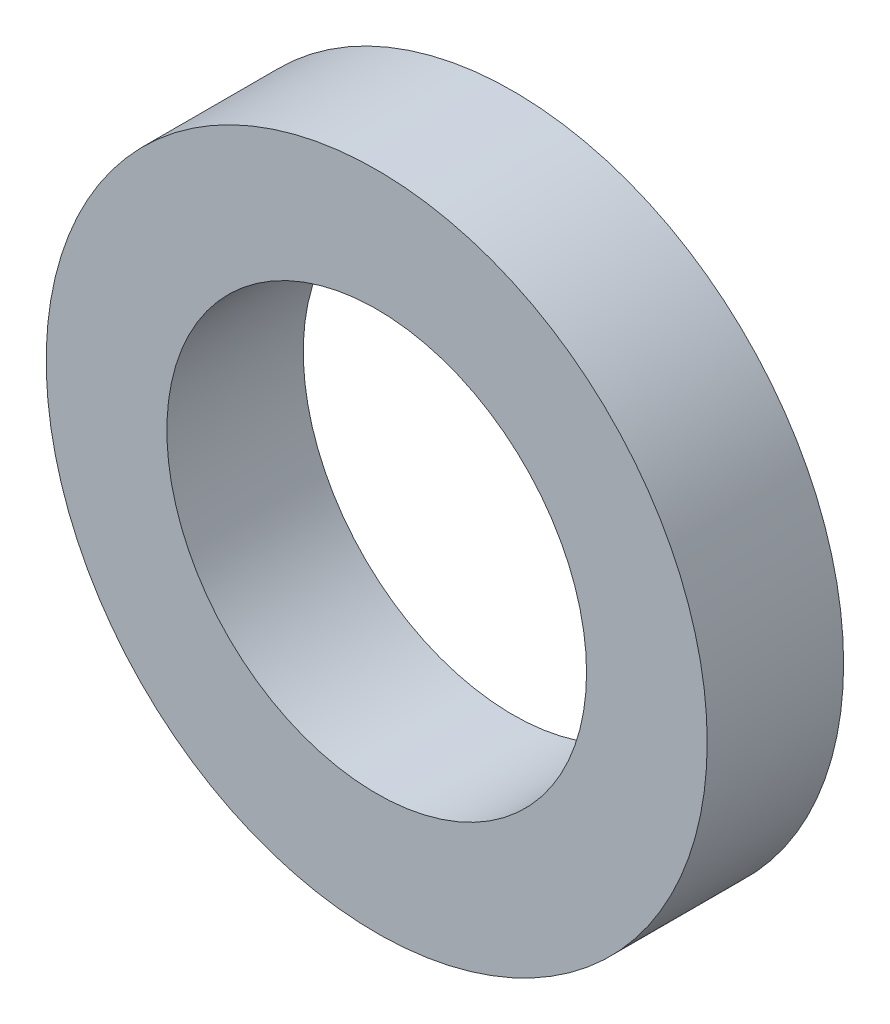
SolidWorks part; units mm, degrees
ref_plane "Front Plane" through (0, 0, 0) normal (0, 0, 1) x (1, 0, 0)
ref_plane "Top Plane" through (0, 0, 0) normal (0, 1, 0) x (1, 0, 0)
ref_plane "Right Plane" through (0, 0, 0) normal (1, 0, 0) x (0, 0, -1)
sketch "Sketch1" plane through (0, 0, 0) normal (0, 0, 1) x (1, 0, 0)
  circle A0 centre (0, 0) radius 12.6
  circle A1 centre (0, 0) radius 8
extrude "Boss-Extrude1" add sketch "Sketch1" along normal blind 5.2
